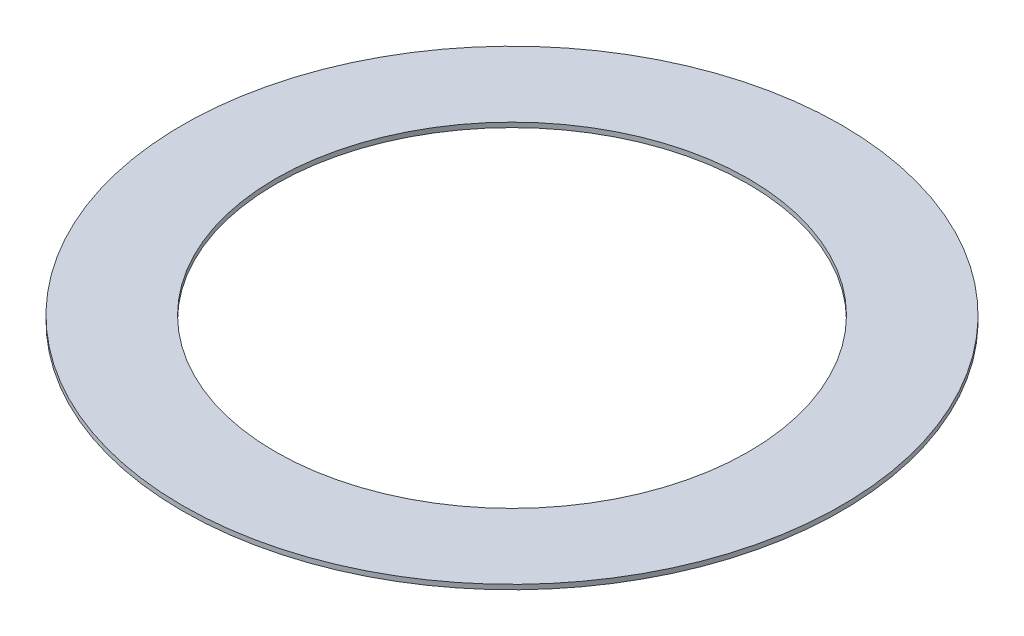
SolidWorks part; units mm, degrees
material "Copper"
ref_plane "Front Plane" through (0, 0, 0) normal (0, 0, 1) x (1, 0, 0)
ref_plane "Top Plane" through (0, 0, 0) normal (0, 1, 0) x (1, 0, 0)
ref_plane "Right Plane" through (0, 0, 0) normal (1, 0, 0) x (0, 0, -1)
sketch "Sketch1" plane through (0, 0, 0) normal (0, 1, 0) x (1, 0, 0)
  circle A0 centre (0, 0) radius 7.5
  circle A1 centre (0, 0) radius 10.45
  dimension "D1" = 15
  dimension "D2" = 20.9
extrude "Extrude1" add sketch "Sketch1" along normal blind 0.15
